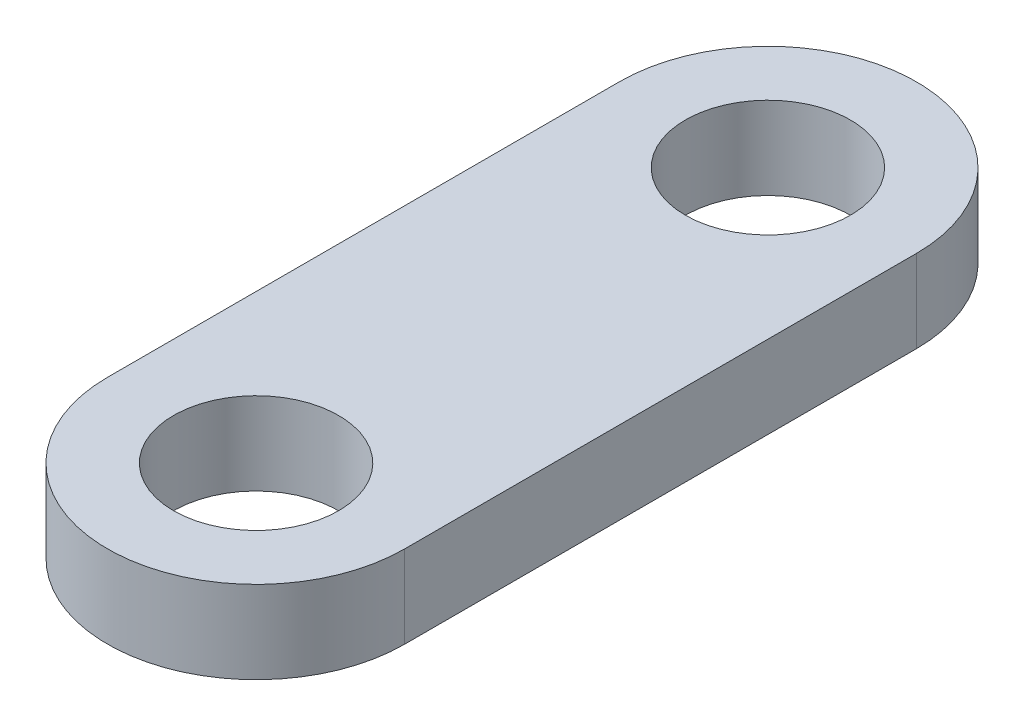
SolidWorks part; units mm, degrees
ref_plane "Front Plane" through (0, 0, 0) normal (0, 0, 1) x (1, 0, 0)
ref_plane "Top Plane" through (0, 0, 0) normal (0, 1, 0) x (1, 0, 0)
ref_plane "Right Plane" through (0, 0, 0) normal (1, 0, 0) x (0, 0, -1)
sketch "Sketch1" plane through (0, 0, 0) normal (0, 1, 0) x (1, 0, 0)
  line L0 (0, 0) -> (0, -31) construction
  line L1 (9, 0) -> (9, -31)
  line L2 (-9, 0) -> (-9, -31)
  circle A0 centre (0, 0) radius 5
  circle A1 centre (0, -31) radius 5
  arc A2 (9, 0) -> (-9, 0) centre (0, 0) ccw
  arc A3 (-9, -31) -> (9, -31) centre (0, -31) ccw
  point P5 (0, -15.5)
  dimension "D2" = 10
  dimension "D3" = 9
  dimension "D1" = 31
extrude "Boss-Extrude1" add sketch "Sketch1" along normal blind 5
